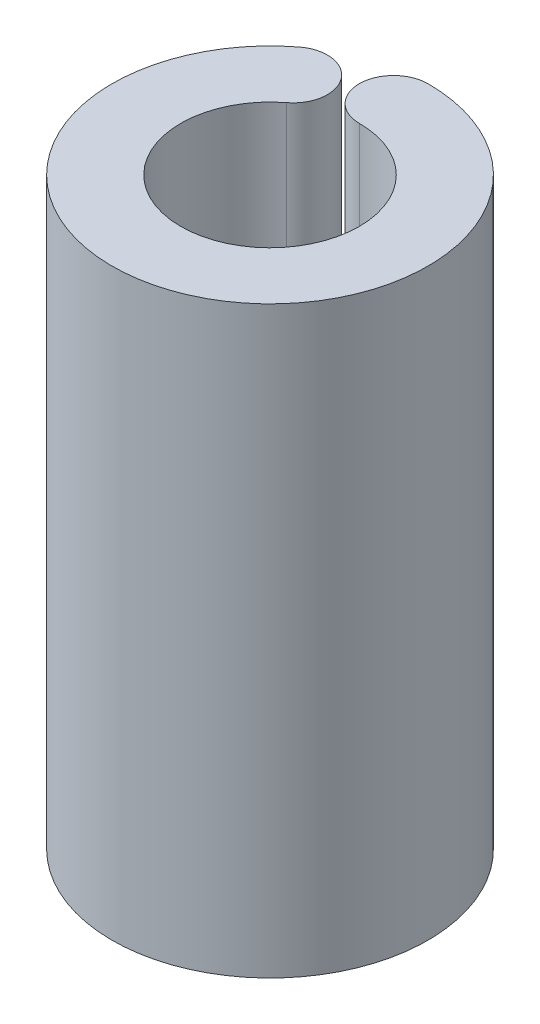
SolidWorks part; units mm, degrees
ref_plane "Front Plane" through (0, 0, 0) normal (0, 0, 1) x (1, 0, 0)
ref_plane "Top Plane" through (0, 0, 0) normal (0, 1, 0) x (1, 0, 0)
ref_plane "Right Plane" through (0, 0, 0) normal (1, 0, 0) x (0, 0, -1)
sketch "Sketch1" plane through (0, 0, 0) normal (0, 1, 0) x (1, 0, 0)
  arc A0 (0, 3.6) -> (-2.1873, 2.8593) centre (0, 0) cw
  arc A1 (0, 2.6) -> (-1.5798, 2.065) centre (0, 0) cw
  arc A2 (0, 4.6) -> (-2.7949, 3.6535) centre (0, 0) cw
  arc A3 (0, 2.6) -> (0, 4.6) centre (0, 3.6) cw
  arc A4 (-1.5798, 2.065) -> (-2.7949, 3.6535) centre (-2.1873, 2.8593) ccw
  dimension "D1" = 3.6
  dimension "D2" = 1
  dimension "D3" = 1
extrude "Boss-Extrude1" add sketch "Sketch1" along normal blind 17
